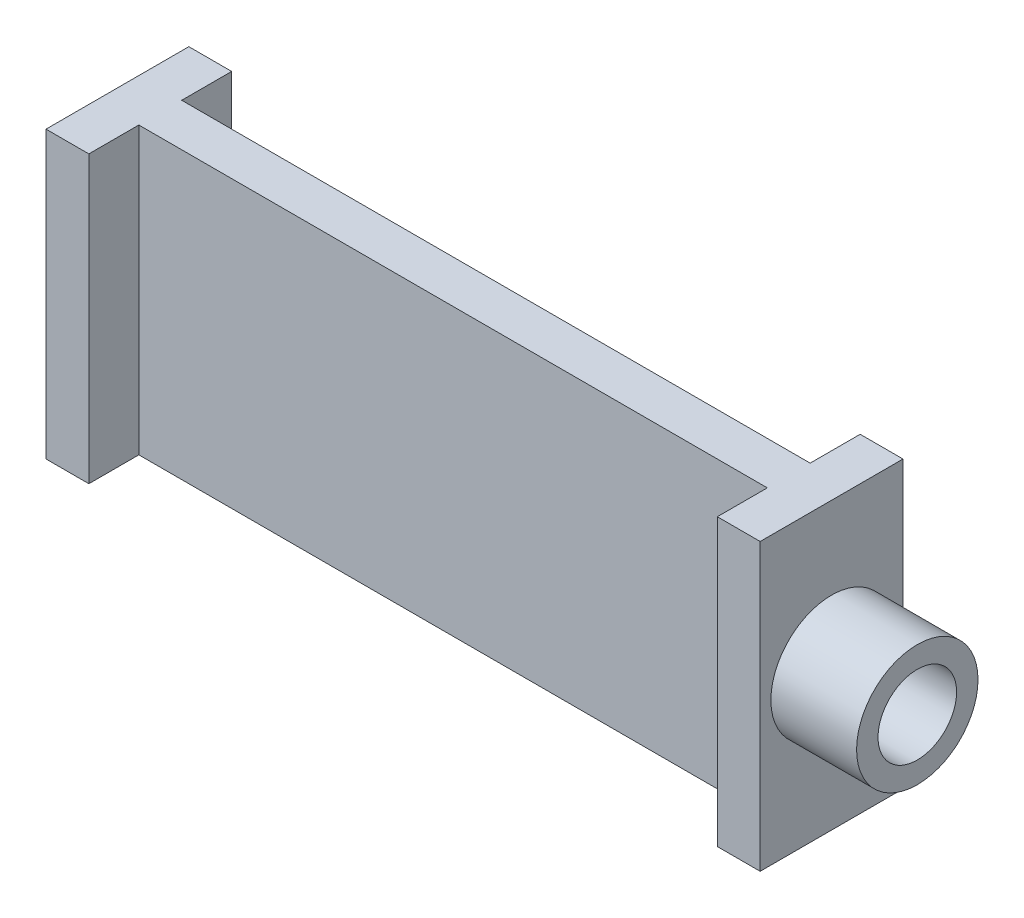
SolidWorks part; units mm, degrees
ref_plane "Front Plane" through (0, 0, 0) normal (0, 0, 1) x (1, 0, 0)
ref_plane "Top Plane" through (0, 0, 0) normal (0, 1, 0) x (1, 0, 0)
ref_plane "Right Plane" through (0, 0, 0) normal (1, 0, 0) x (0, 0, -1)
sketch "Sketch1" plane through (0, 0, 0) normal (0, 1, 0) x (1, 0, 0)
  line L0 (0, 0) -> (0, 20)
  line L5 (0, 20) -> (6, 20)
  line L6 (6, 20) -> (6, 13)
  line L7 (6, 13) -> (94, 13)
  line L8 (94, 13) -> (94, 20)
  line L9 (94, 20) -> (100, 20)
  line L10 (100, 20) -> (100, 0)
  line L11 (100, 0) -> (94, 0)
  line L12 (94, 0) -> (94, 7)
  line L13 (94, 7) -> (6, 7)
  line L14 (6, 7) -> (6, 0)
  line L15 (6, 0) -> (0, 0)
  line L18 (6, 10) -> (93, 10) construction
  line L19 (6, 13) -> (6, 7) construction
  line L20 (94, 13) -> (94, 7) construction
  point P11 (49.5, 10)
  dimension "D1" = 100
  dimension "D2" = 6
  dimension "D3" = 6
  dimension "D4" = 6
  dimension "D5" = 6
  dimension "D6" = 20
extrude "Boss-Extrude2" add sketch "Sketch1" along normal blind 40
sketch "Sketch2" plane through (100, 0, 0) normal (1, 0, 0) x (0, 0, -1)
  line L0 (0, 40) -> (20, 0) construction
  line L1 (0, 0) -> (20, 40) construction
  circle A0 centre (10, 20) radius 8.5
  circle A1 centre (10, 20) radius 5.5
  point P12 (10, 20)
  dimension "D1" = 17
  dimension "D2" = 3
extrude "Boss-Extrude3" add sketch "Sketch2" along normal blind 12
sketch "Sketch3" plane through (112, 0, 0) normal (1, 0, 0) x (0, 0, -1)
  line L0 (1.5, 20) -> (18.5, 20)
  circle A1 centre (10, 20) radius 8.5 construction
sketch "Sketch4" plane through (0, 0, -7) normal (0, 0, 1) x (1, 0, 0)
  line L0 (94, 20) -> (6, 20)
  line L1 (94, 40) -> (94, 0) construction
  line L2 (6, 40) -> (6, 0) construction
